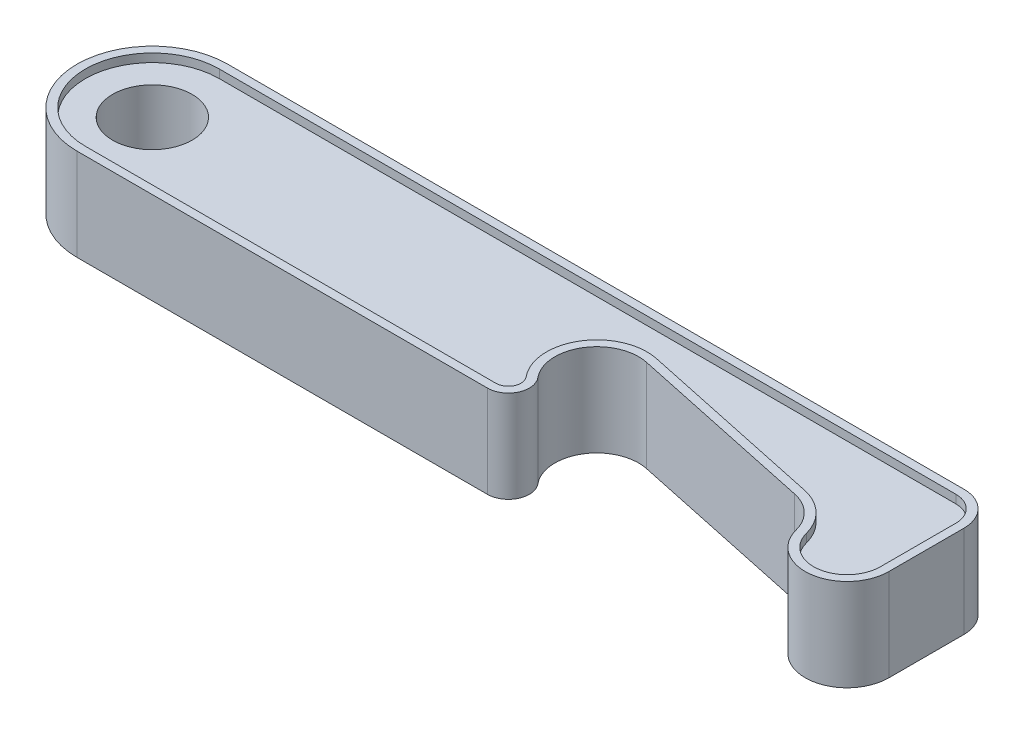
SolidWorks part; units mm, degrees
ref_plane "Front Plane" through (0, 0, 0) normal (0, 0, 1) x (1, 0, 0)
ref_plane "Top Plane" through (0, 0, 0) normal (0, 1, 0) x (1, 0, 0)
ref_plane "Right Plane" through (0, 0, 0) normal (1, 0, 0) x (0, 0, -1)
sketch "Sketch1" plane through (0, 0, 0) normal (0, 1, 0) x (1, 0, 0)
  line L0 (55.8571, 3.1733) -> (78.3571, -1.6093)
  line L5 (0, -9) -> (49.0402, -9)
  line L7 (0, 9) -> (88, 9)
  line L8 (92, -4) -> (92, 5)
  circle A1 centre (0, 0) radius 4.75
  arc A2 (0, 9) -> (0, -9) centre (0, 0) ccw
  arc A3 (55.8571, 3.1733) -> (50.966, -4.9058) centre (54.8175, -1.7175) ccw
  arc A4 (82.1588, -5.25) -> (78.3571, -1.6093) centre (77.3175, -6.5) ccw
  arc A5 (82.1588, -5.25) -> (92, -4) centre (87, -4) ccw
  arc A6 (49.0402, -9) -> (50.966, -4.9058) centre (49.0402, -6.5) ccw
  arc A7 (88, 9) -> (92, 5) centre (88, 5) cw
  point P0 (0, 0)
  point P15 (0, 0)
  dimension "D3" = 92
  dimension "D1" = 9.5
  dimension "D2" = 18
  dimension "D4" = 10
  dimension "D5" = 10
  dimension "D8" = 10
  dimension "D9" = 5
  dimension "D10" = 4
  dimension "D6" = 22.5
  dimension "D7" = 12
extrude "Boss-Extrude1" add sketch "Sketch1" along normal blind 9
sketch "Sketch2" plane through (0, 9, 0) normal (0, 1, 0) x (1, 0, 0)
  line L0 (88, 8) -> (0, 8)
  line L1 (0, -8) -> (49.0402, -8)
  line L2 (56.065, 4.1514) -> (78.565, -0.6311)
  line L3 (91, -4) -> (91, 5)
  line L4 (0, -9) -> (49.0402, -9)
  line L5 (55.8571, 3.1733) -> (78.3571, -1.6093)
  line L6 (92, -4) -> (92, 5)
  line L7 (88, 9) -> (0, 9)
  line L8 (0, -9) -> (49.0402, -9)
  line L9 (55.8571, 3.1733) -> (78.3571, -1.6093)
  line L10 (92, -4) -> (92, 5)
  line L11 (88, 9) -> (0, 9)
  arc A0 (0, 8) -> (0, -8) centre (0, 0) ccw
  arc A1 (49.0402, -8) -> (50.1957, -5.5435) centre (49.0402, -6.5) ccw
  arc A2 (56.065, 4.1514) -> (50.1957, -5.5435) centre (54.8175, -1.7175) ccw
  arc A3 (83.127, -5) -> (78.565, -0.6311) centre (77.3175, -6.5) ccw
  arc A4 (83.127, -5) -> (91, -4) centre (87, -4) ccw
  arc A5 (91, 5) -> (88, 8) centre (88, 5) ccw
  arc A6 (0, 9) -> (0, -9) centre (0, 0) ccw
  arc A7 (49.0402, -9) -> (50.966, -4.9058) centre (49.0402, -6.5) ccw
  arc A8 (55.8571, 3.1733) -> (50.966, -4.9058) centre (54.8175, -1.7175) ccw
  arc A9 (82.1588, -5.25) -> (78.3571, -1.6093) centre (77.3175, -6.5) ccw
  arc A10 (82.1588, -5.25) -> (92, -4) centre (87, -4) ccw
  arc A11 (92, 5) -> (88, 9) centre (88, 5) ccw
  arc A12 (0, 9) -> (0, -9) centre (0, 0) ccw
  arc A13 (49.0402, -9) -> (50.966, -4.9058) centre (49.0402, -6.5) ccw
  arc A14 (55.8571, 3.1733) -> (50.966, -4.9058) centre (54.8175, -1.7175) ccw
  arc A15 (82.1588, -5.25) -> (78.3571, -1.6093) centre (77.3175, -6.5) ccw
  arc A16 (82.1588, -5.25) -> (92, -4) centre (87, -4) ccw
  arc A17 (92, 5) -> (88, 9) centre (88, 5) ccw
  dimension "D1" = 0
  dimension "D2" = 1
extrude "Boss-Extrude2" add sketch "Sketch2" along normal blind 1
sketch "Sketch3" plane through (0, 0, 0) normal (0, -1, 0) x (1, 0, 0)
  line L0 (49.0402, 8) -> (0, 8)
  line L1 (0, -8) -> (88, -8)
  line L2 (91, -5) -> (91, 4)
  line L3 (78.565, 0.6311) -> (56.065, -4.1514)
  line L4 (0, -9) -> (88, -9)
  line L5 (92, -5) -> (92, 4)
  line L6 (78.3571, 1.6093) -> (55.8571, -3.1733)
  line L7 (49.0402, 9) -> (0, 9)
  line L8 (0, -9) -> (88, -9)
  line L9 (92, -5) -> (92, 4)
  line L10 (78.3571, 1.6093) -> (55.8571, -3.1733)
  line L11 (49.0402, 9) -> (0, 9)
  arc A0 (0, 8) -> (0, -8) centre (0, 0) ccw
  arc A1 (88, -8) -> (91, -5) centre (88, -5) ccw
  arc A2 (91, 4) -> (83.127, 5) centre (87, 4) ccw
  arc A3 (78.565, 0.6311) -> (83.127, 5) centre (77.3175, 6.5) ccw
  arc A4 (50.1957, 5.5435) -> (56.065, -4.1514) centre (54.8175, 1.7175) ccw
  arc A5 (50.1957, 5.5435) -> (49.0402, 8) centre (49.0402, 6.5) ccw
  arc A6 (0, 9) -> (0, -9) centre (0, 0) ccw
  arc A7 (88, -9) -> (92, -5) centre (88, -5) ccw
  arc A8 (92, 4) -> (82.1588, 5.25) centre (87, 4) ccw
  arc A9 (78.3571, 1.6093) -> (82.1588, 5.25) centre (77.3175, 6.5) ccw
  arc A10 (50.966, 4.9058) -> (55.8571, -3.1733) centre (54.8175, 1.7175) ccw
  arc A11 (50.966, 4.9058) -> (49.0402, 9) centre (49.0402, 6.5) ccw
  arc A12 (0, 9) -> (0, -9) centre (0, 0) ccw
  arc A13 (88, -9) -> (92, -5) centre (88, -5) ccw
  arc A14 (92, 4) -> (82.1588, 5.25) centre (87, 4) ccw
  arc A15 (78.3571, 1.6093) -> (82.1588, 5.25) centre (77.3175, 6.5) ccw
  arc A16 (50.966, 4.9058) -> (55.8571, -3.1733) centre (54.8175, 1.7175) ccw
  arc A17 (50.966, 4.9058) -> (49.0402, 9) centre (49.0402, 6.5) ccw
  dimension "D1" = 0
  dimension "D2" = 1
extrude "Boss-Extrude3" add sketch "Sketch3" along normal blind 1
